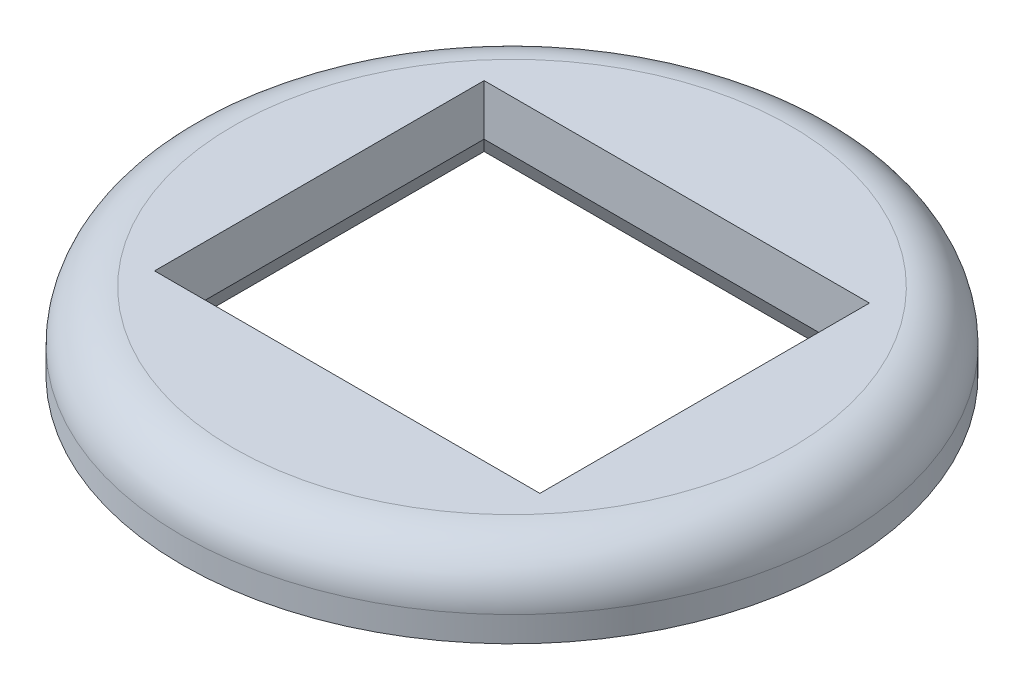
SolidWorks part; units mm, degrees
ref_plane "Спереди" through (0, 0, 0) normal (0, 0, 1) x (1, 0, 0)
ref_plane "Сверху" through (0, 0, 0) normal (0, 1, 0) x (1, 0, 0)
ref_plane "Справа" through (0, 0, 0) normal (1, 0, 0) x (0, 0, -1)
sketch "Sketch1" plane through (0, 0, 0) normal (0, 1, 0) x (1, 0, 0)
  line L1 (7.6, -6.5) -> (-7.6, -6.5)
  line L2 (7.6, -6.5) -> (7.6, 6.5)
  line L3 (7.6, 6.5) -> (-7.6, 6.5)
  line L4 (-7.6, -6.5) -> (-7.6, 6.5)
  line L5 (7.6, -6.5) -> (-7.6, 6.5) construction
  line L6 (7.6, 6.5) -> (-7.6, -6.5) construction
  circle A0 centre (0, 0) radius 13
  dimension "D3" = 26
  dimension "D1" = 15.2
  dimension "D2" = 13
extrude "Boss-Extrude1" add sketch "Sketch1" along normal blind 3
fillet "Fillet1" radius 2 1 edges at (0, 3, 13)
chamfer "Chamfer1" distance 1 angle 30 4 edges at (7.6, 0, 0) (0, 0, 6.5) (-7.6, 0, 0) (0, 0, -6.5)
